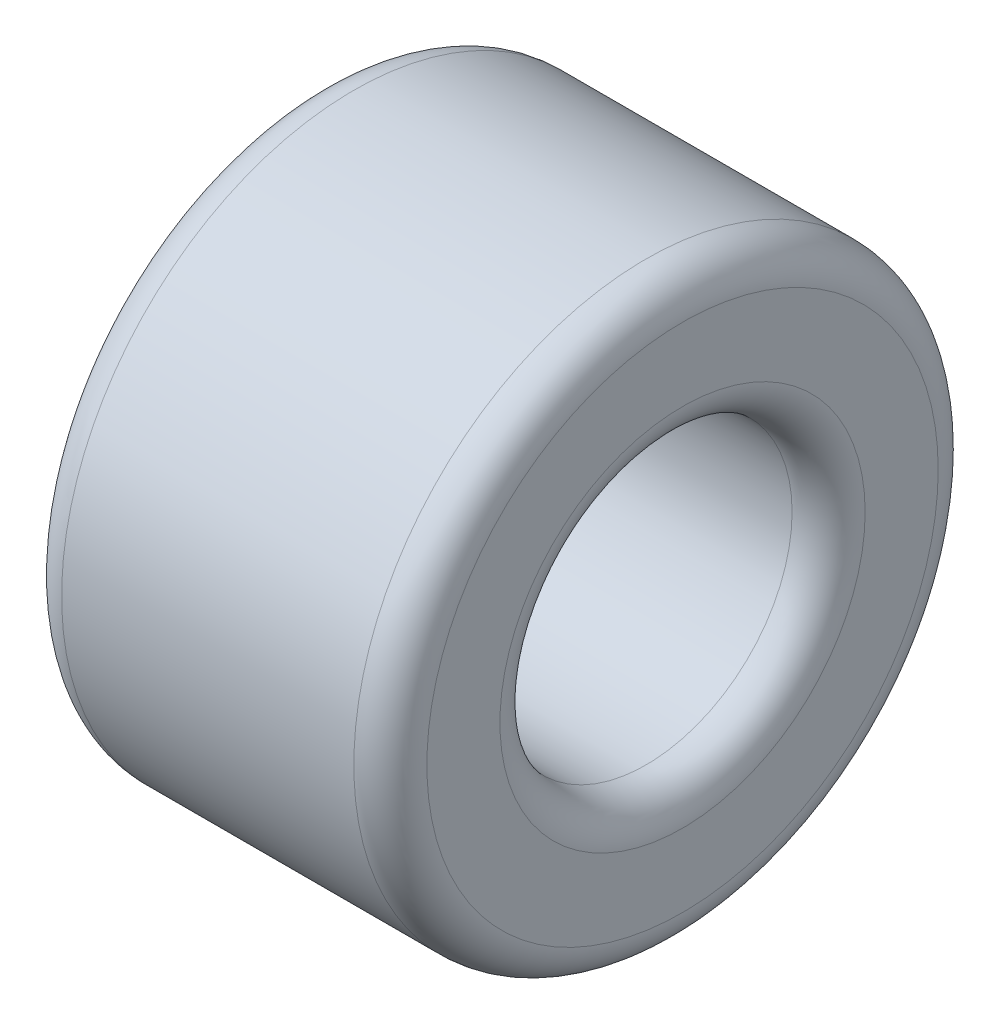
SolidWorks part; units mm, degrees
ref_plane "前视基准面" through (0, 0, 0) normal (0, 0, 1) x (1, 0, 0)
ref_plane "上视基准面" through (0, 0, 0) normal (0, 1, 0) x (1, 0, 0)
ref_plane "右视基准面" through (0, 0, 0) normal (1, 0, 0) x (0, 0, -1)
other "Configuration Table"
sketch "草图1" plane through (0, 0, 0) normal (1, 0, 0) x (0, 0, -1)
  circle A0 centre (0, 0) radius 4
  circle A1 centre (0, 0) radius 8
  dimension "D1" = 8
  dimension "D2" = 16
extrude "凸台-拉伸1" add sketch "草图1" along normal mid plane 10
fillet "圆角1" radius 1 4 edges at (-5, 0, -4) (-5, 0, -8) (5, 0, -8) (5, 0, -4)
